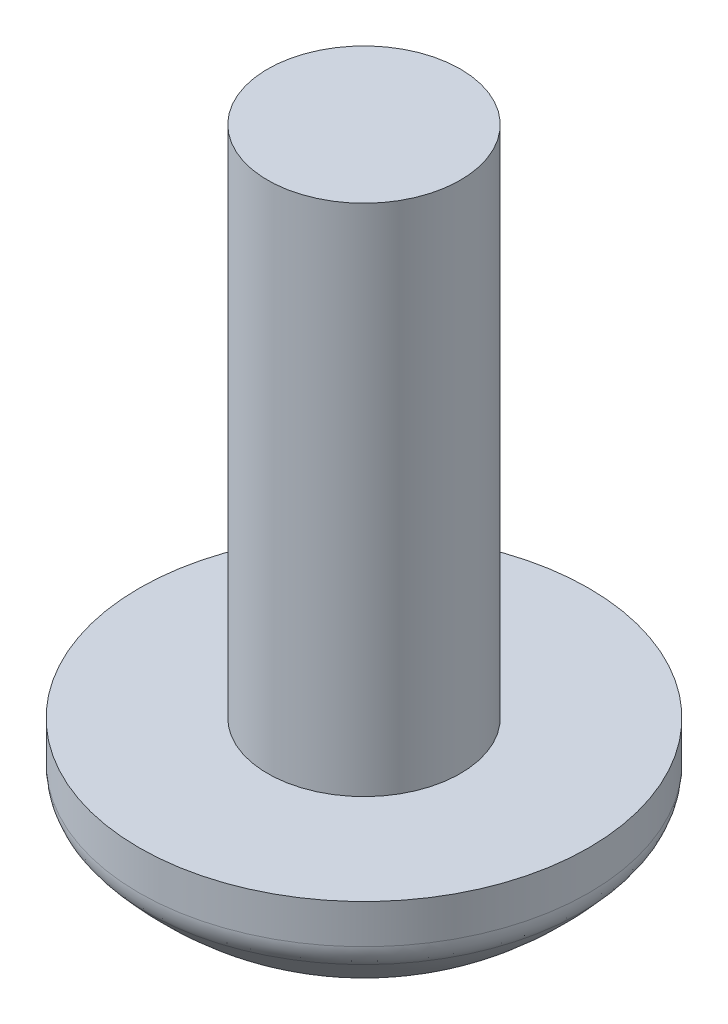
SolidWorks part; units mm, degrees
material "普通碳钢"
ref_plane "Front" through (0, 0, 0) normal (0, 0, 1) x (1, 0, 0)
ref_plane "Top" through (0, 0, 0) normal (0, 1, 0) x (1, 0, 0)
ref_plane "Right" through (0, 0, 0) normal (1, 0, 0) x (0, 0, -1)
sketch "草图2" plane through (0, 0, 0) normal (1, 0, 0) x (0, 0, -1)
  line L0 (1.8178, -1.252) -> (1.1778, -2.0258) construction
  line L1 (1.8178, -0.4597) -> (-0.1822, -0.4597)
  line L2 (1.8178, -0.4597) -> (1.8178, -1.252)
  line L4 (-1.6822, -0.4597) -> (-1.6822, -2.9597)
  line L6 (-1.6822, -0.4597) -> (-1.6822, 7.5403)
  line L7 (-1.6822, 7.5403) -> (-0.1822, 7.5403)
  line L8 (-0.1822, -0.4597) -> (-0.1822, 7.5403)
  line L9 (1.1778, -2.0258) -> (0.3066, -2.8406) construction
  line L10 (0.3066, -2.8406) -> (-1.6822, -2.9597) construction
  spline S0 degree 3 poles (1.8178, -1.252) (1.1778, -2.0258) (0.3066, -2.8406) (-1.6822, -2.9597) knots 0 0 0 0 1 1 1 1
  dimension "D1" = 1.5
  dimension "D2" = 2.5
  dimension "D3" = 8
  dimension "D4" = 8
revolve "旋转1" add sketch "草图2" angle 360 about L6
cosmetic thread "装饰螺纹线1" parameters "D2"=2
fillet "圆角1" radius 0.5 1 edges at (0, -1.252, -1.8178)
ref_plane "基准面1" through (0, -2.9597, 0) normal (0, -1, 0) x (-1, 0, 0)
sketch "草图3" plane through (0, -2.9597, 0) normal (0, -1, 0) x (-1, 0, 0)
  line L0 (-0.4708, -1.1822) -> (-2.75, -1.1822)
  line L1 (2.75, -2.1822) -> (0.5292, -2.1822)
  line L2 (2.75, -2.1822) -> (2.75, -1.1822)
  line L3 (2.75, -1.1822) -> (0.5292, -1.1822)
  line L4 (-2.75, -2.1822) -> (-2.75, -1.1822)
  line L6 (0.0292, -1.6769) -> (0, -1.6822) construction
  line L7 (0.5292, -4.4269) -> (-0.4708, -4.4269)
  line L8 (0.5292, -4.4269) -> (0.5292, -2.1822)
  line L9 (0.5292, 1.0731) -> (-0.4708, 1.0731)
  line L10 (-0.4708, -4.4269) -> (-0.4708, -2.1822)
  line L13 (0.0292, -1.6769) -> (0.0274, -1.6872) construction
  line L15 (0.5292, -1.1822) -> (0.5292, 1.0731)
  line L16 (0.0312, -1.6879) -> (0, -1.6822) construction
  line L17 (0.0312, -1.6879) -> (0.0292, -1.6769) construction
  line L20 (-0.4708, -1.1822) -> (-0.4708, 1.0731)
  line L21 (-0.4708, -2.1822) -> (-2.75, -2.1822)
  point P0 (0, -1.6822)
  point P6 (0.0292, -1.6769)
  dimension "D1" = 1
  dimension "D2" = 1
  dimension "D3" = 5.5
  dimension "D4" = 5.5
extrude "切除-拉伸1" cut sketch "草图3" against normal blind 1.5
